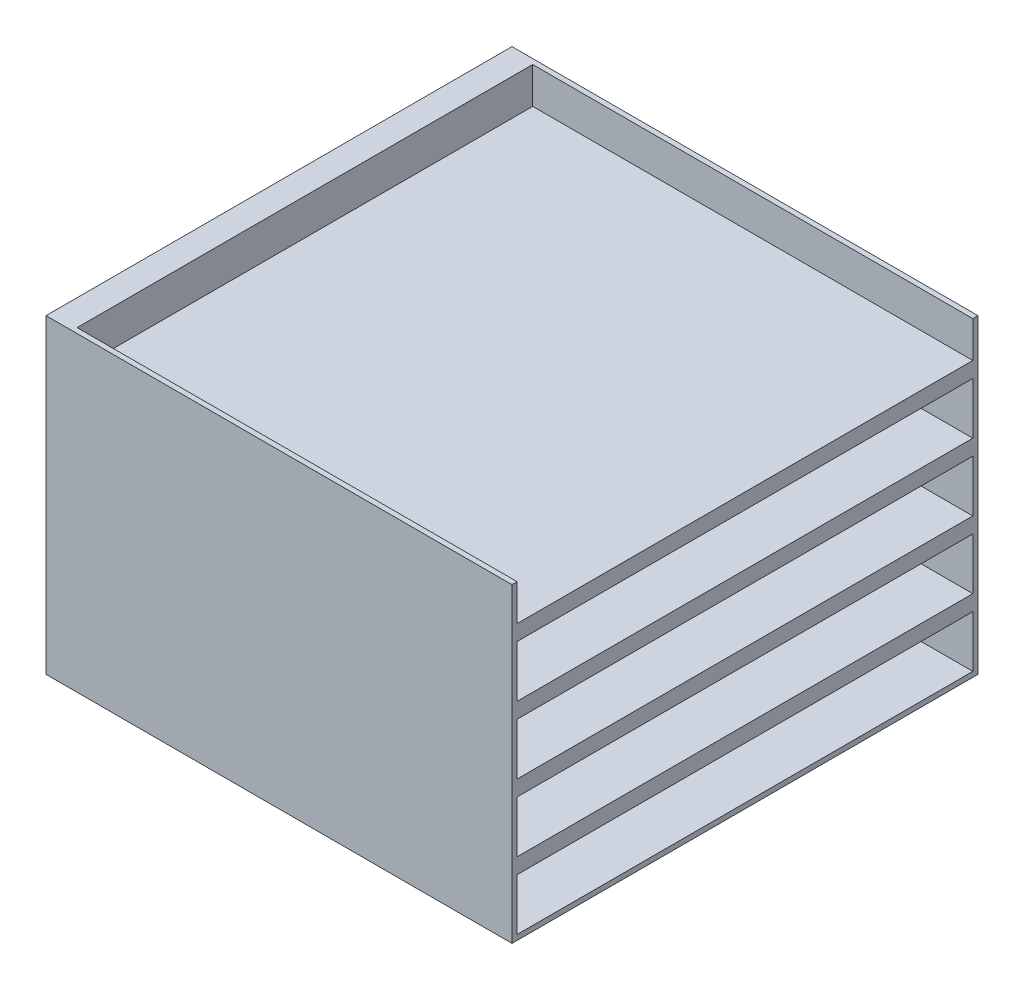
SolidWorks part; units mm, degrees
ref_plane "Front Plane" through (0, 0, 0) normal (0, 0, 1) x (1, 0, 0)
ref_plane "Top Plane" through (0, 0, 0) normal (0, 1, 0) x (1, 0, 0)
ref_plane "Right Plane" through (0, 0, 0) normal (1, 0, 0) x (0, 0, -1)
sketch "Sketch1" plane through (0, 0, 0) normal (0, 1, 0) x (1, 0, 0)
  line L1 (-450, 450) -> (450, 450)
  line L2 (-450, 450) -> (-450, -450)
  line L3 (-450, -450) -> (450, -450)
  line L4 (450, 450) -> (450, -450)
  line L5 (-450, 450) -> (450, -450) construction
  line L6 (-450, -450) -> (450, 450) construction
  point P0 (0, 0)
  dimension "D1" = 900
  dimension "D2" = 900
extrude "Boss-Extrude1" add sketch "Sketch1" along normal blind 600
sketch "Sketch3" plane through (450, 0, 0) normal (1, 0, 0) x (0, 0, -1)
  line L0 (0, 600) -> (0, 0) construction
  line L1 (-450, 600) -> (450, 600) construction
  line L2 (-450, 0) -> (450, 0) construction
  line L3 (440, 110) -> (-440, 110)
  line L4 (440, 110) -> (440, 10)
  line L5 (440, 10) -> (-440, 10)
  line L6 (-440, 110) -> (-440, 10)
  line L7 (440, 110) -> (-440, 10) construction
  line L8 (440, 10) -> (-440, 110) construction
  line L9 (450, 600) -> (450, 0) construction
  line L10 (440, 240) -> (-440, 240)
  line L11 (440, 140) -> (-440, 140)
  line L12 (-440, 240) -> (-440, 140)
  line L13 (440, 240) -> (440, 140)
  line L14 (440, 370) -> (-440, 370)
  line L15 (440, 270) -> (-440, 270)
  line L16 (-440, 370) -> (-440, 270)
  line L17 (440, 370) -> (440, 270)
  line L18 (440, 500) -> (-440, 500)
  line L19 (440, 400) -> (-440, 400)
  line L20 (-440, 500) -> (-440, 400)
  line L21 (440, 500) -> (440, 400)
  line L22 (440, 630) -> (-440, 630)
  line L23 (440, 530) -> (-440, 530)
  line L24 (-440, 630) -> (-440, 530)
  line L25 (440, 630) -> (440, 530)
  point P5 (0, 60)
  dimension "D1" = 10
  dimension "D2" = 10
  dimension "D3" = 100
  dimension "D4" = 5
extrude "Cut-Extrude2" cut sketch "Sketch3" along direction (1, 0, 0) on the side against the normal blind 850
